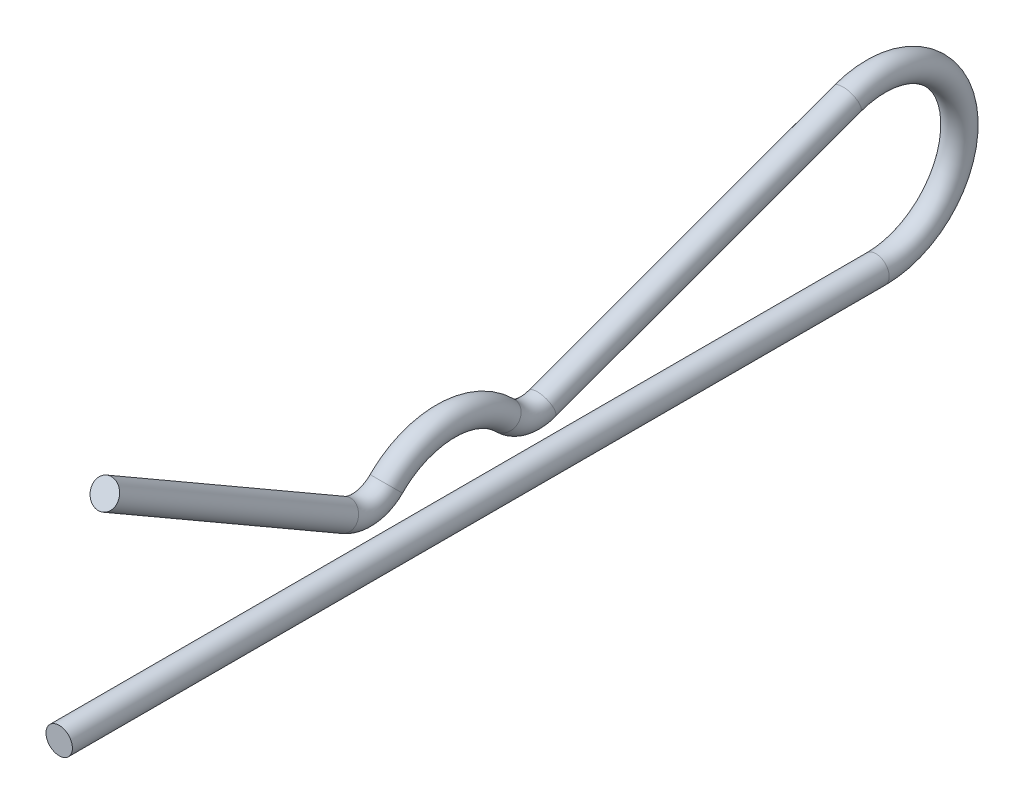
SolidWorks part; units mm, degrees
ref_plane "Front" through (0, 0, 0) normal (0, 0, 1) x (1, 0, 0)
ref_plane "Top" through (0, 0, 0) normal (0, 1, 0) x (1, 0, 0)
ref_plane "Right" through (0, 0, 0) normal (1, 0, 0) x (0, 0, -1)
sketch "Sketch1" plane through (0, 0, 0) normal (1, 0, 0) x (0, 0, -1)
  line L0 (-20.6375, -3.7719) -> (16.2687, -3.7719) construction
  line L1 (-6.9824, 0) -> (0.6324, 0) construction
  line L2 (20.6375, -3.7719) -> (20.6375, 0) construction
  line L3 (20.6375, 0) -> (20.0406, 0) construction
  line L4 (-20.6375, -3.7719) -> (-20.6375, -3.175) construction
  line L5 (20.6375, -3.7719) -> (-20.6375, -3.7719) construction
  line L6 (-7.7761, -1.3748) -> (-18.5738, 4.8592) construction
  line L7 (-3.175, 0) -> (-3.175, -3.7719) construction
  line L8 (-20.6375, -3.7719) -> (-20.6375, -4.3688) construction
  line L9 (20.6375, -3.7719) -> (20.6375, 3.7719) construction
  line L10 (20.6375, 3.7719) -> (-20.6375, 3.7719) construction
  line L11 (-20.6375, 3.7719) -> (-20.6375, -3.7719) construction
  line L12 (0, 3.7719) -> (0, -3.7719) construction
  line L13 (14.9759, 3.5434) -> (1.1765, -1.4913) construction
  circle A0 centre (16.2687, 0) radius 3.175 construction
  arc A1 (-0.4954, -1.1173) -> (-5.8546, -1.1173) centre (-3.175, -3.7719) ccw construction
  arc A6 (-5.8546, -1.1173) -> (-7.7761, -1.3748) centre (-6.9824, 0) cw construction
  arc A8 (1.1765, -1.4913) -> (-0.4954, -1.1173) centre (0.6324, 0) cw construction
  arc A9 (16.2687, -3.7719) -> (14.9759, 3.5434) centre (16.2687, 0) ccw construction
  point P2 (0, 0)
  dimension "D1" = 1.5875
  dimension "Eye Diameter" = 6.35
  dimension "D2" = 17.4625
  dimension "D5" = 2.0638
  dimension "D9" = 30
  dimension "D11" = 0.5969
  dimension "D3" = 0.5969
  dimension "Length" = 41.275
  dimension "Wire Diameter" = 1.1938
ref_plane "Plane1" through (0, 0, 20.6375) normal (0, 0, 1) x (1, 0, 0)
sketch "Sketch3" plane through (0, 0, 20.6375) normal (0, 0, 1) x (1, 0, 0)
  circle A0 centre (0, -3.7719) radius 0.5969
sketch "Sketch4" plane through (0, 0, 0) normal (1, 0, 0) x (0, 0, -1)
  line L0 (-7.7761, -1.3748) -> (-18.5738, 4.8592) construction
  line L1 (14.9759, 3.5434) -> (1.1765, -1.4913) construction
  line L2 (-20.6375, -3.7719) -> (16.2687, -3.7719) construction
  line L3 (-7.7761, -1.3748) -> (-18.5738, 4.8592)
  line L4 (14.9759, 3.5434) -> (1.1765, -1.4913)
  line L5 (-20.6375, -3.7719) -> (16.2687, -3.7719)
  arc A0 (-7.7761, -1.3748) -> (-5.8546, -1.1173) centre (-6.9824, 0) ccw construction
  arc A1 (-0.4954, -1.1173) -> (-5.8546, -1.1173) centre (-3.175, -3.7719) ccw construction
  arc A2 (-0.4954, -1.1173) -> (1.1765, -1.4913) centre (0.6324, 0) ccw construction
  arc A3 (16.2687, -3.7719) -> (14.9759, 3.5434) centre (16.2687, 0) ccw construction
  arc A4 (-7.7761, -1.3748) -> (-5.8546, -1.1173) centre (-6.9824, 0) ccw
  arc A5 (-0.4954, -1.1173) -> (-5.8546, -1.1173) centre (-3.175, -3.7719) ccw
  arc A6 (-0.4954, -1.1173) -> (1.1765, -1.4913) centre (0.6324, 0) ccw
  arc A7 (16.2687, -3.7719) -> (14.9759, 3.5434) centre (16.2687, 0) ccw
sweep "Sweep1" add profiles "Sketch3" path "Sketch4"
equation "\"D11@Sketch1\" = \"Wire Diameter@Sketch1\" / 2"
equation "\"D1@Sketch1\" = \"Eye Diameter@Sketch1\" / 4"
equation "\"D3@Sketch1\" = \"D11@Sketch1\""
equation "\"D2@Sketch1\" =  ( \"Length@Sketch1\" - \"Eye Diameter@Sketch1\" )  / 2"
equation "\"D5@Sketch1\" = \"Length@Sketch1\" * .05"
